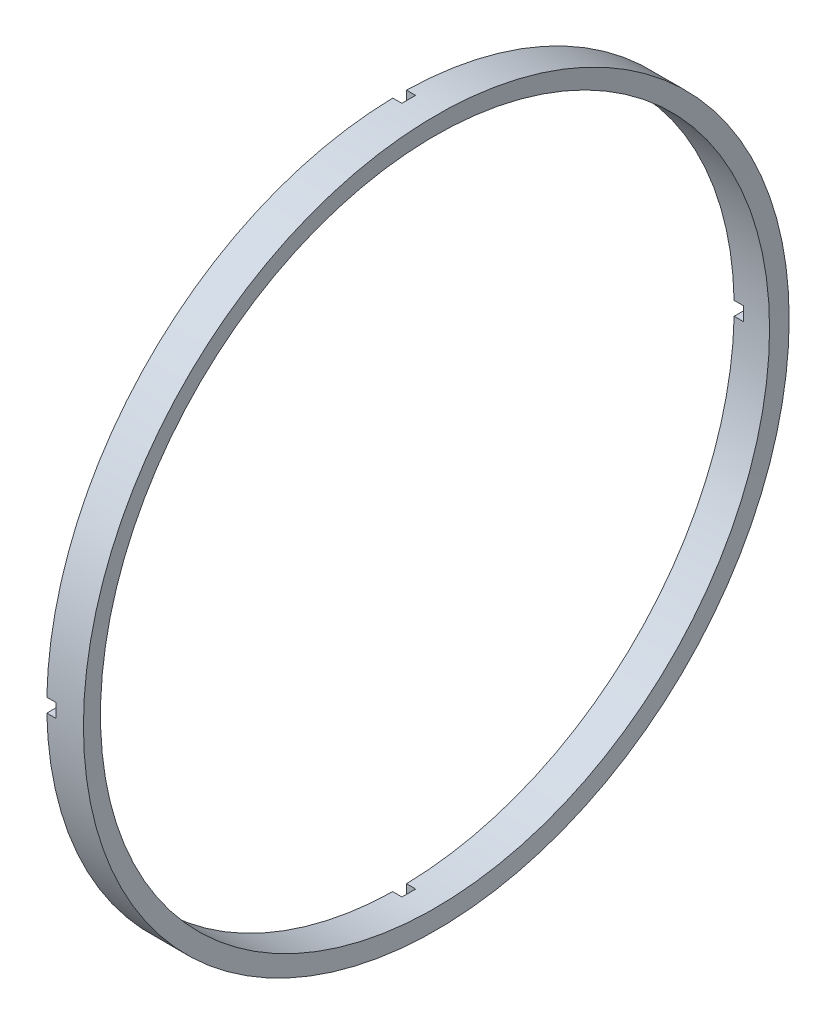
SolidWorks part; units mm, degrees
material "2018 slitina"
ref_plane "Přední rovina" through (0, 0, 0) normal (0, 0, 1) x (1, 0, 0)
ref_plane "Horní rovina" through (0, 0, 0) normal (0, 1, 0) x (1, 0, 0)
ref_plane "Pravá rovina" through (0, 0, 0) normal (1, 0, 0) x (0, 0, -1)
sketch "Skica1" plane through (0, 0, 0) normal (0, 0, 1) x (1, 0, 0)
  line L0 (-23.644, 38.5) -> (-23.644, 36.5)
  line L2 (-23.644, 36.5) -> (-19.7838, 36.5)
  line L3 (-19.7838, 36.5) -> (-19.644, 38.5)
  line L4 (-19.644, 38.5) -> (-23.644, 38.5)
  line L5 (-19.6789, 38) -> (-19.7838, 36.5) construction
  line L6 (0, 0) -> (-61.6382, 0) construction
  dimension "D1" = 77
  dimension "D2" = 4
  dimension "D3" = 2
revolve "Rotovat1" add sketch "Skica1" angle 360 about L6
cosmetic thread "Kosmetický závit1" parameters "D2"=76.18
sketch "Skica2" plane through (-23.644, 0, 0) normal (-1, 0, 0) x (0, 0, 1)
  line L1 (-0.75, -38.5) -> (0.75, -38.5)
  line L2 (-0.75, -38.5) -> (-0.75, 38.5)
  line L3 (-0.75, 38.5) -> (0.75, 38.5)
  line L4 (0.75, -38.5) -> (0.75, 38.5)
  line L5 (-0.75, -38.5) -> (0.75, 38.5) construction
  line L6 (-0.75, 38.5) -> (0.75, -38.5) construction
  line L7 (-38.5, -0.75) -> (38.5, -0.75)
  line L8 (-38.5, -0.75) -> (-38.5, 0.75)
  line L9 (-38.5, 0.75) -> (38.5, 0.75)
  line L10 (38.5, -0.75) -> (38.5, 0.75)
  line L11 (-38.5, -0.75) -> (38.5, 0.75) construction
  line L12 (-38.5, 0.75) -> (38.5, -0.75) construction
  circle A0 centre (0, 0) radius 38.5 construction
  point P0 (0, 0)
  point P8 (0, 0)
  circle M5 centre (0, 0) radius 36.5
  dimension "D1" = 1.5
extrude "Odebrat vysunutím1" cut sketch "Skica2" against normal blind 1 contours L2 L9 L4 M5 | L9 L4 L7 M5
